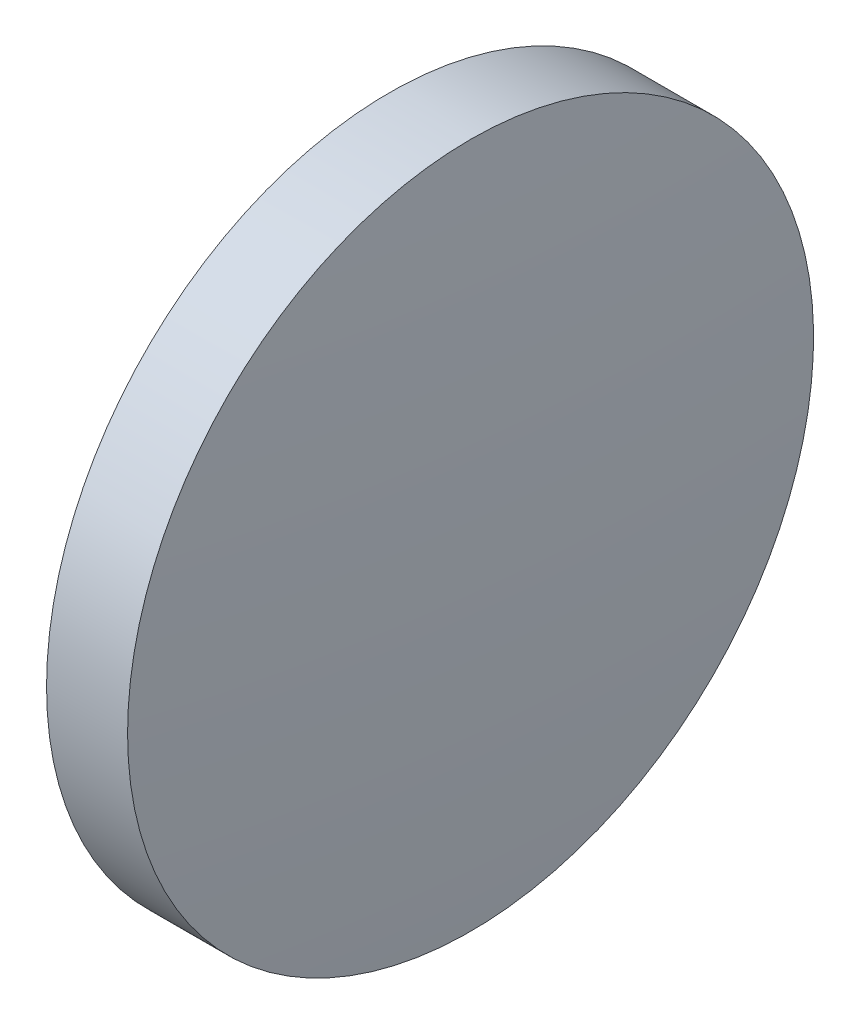
SolidWorks part; units mm, degrees
ref_plane "前视基准面" through (0, 0, 0) normal (0, 0, 1) x (1, 0, 0)
ref_plane "上视基准面" through (0, 0, 0) normal (0, 1, 0) x (1, 0, 0)
ref_plane "右视基准面" through (0, 0, 0) normal (1, 0, 0) x (0, 0, -1)
sketch "草图1" plane through (0, 0, 0) normal (0, 0, 1) x (1, 0, 0)
  line L0 (110.1654, 65.2336) -> (128.9614, 65.2336) construction
  line L1 (115.7736, 65.2336) -> (115.7736, 77.9336)
  line L2 (115.7736, 77.9336) -> (118.7739, 77.9336)
  line L3 (119.2126, 65.2336) -> (115.7736, 65.2336)
  arc A0 (119.2126, 65.2336) -> (118.7739, 77.9336) centre (-64.8184, 65.2336) ccw
  dimension "D1" = 184.031
revolve "旋转1" add sketch "草图1" angle 360 about L0
